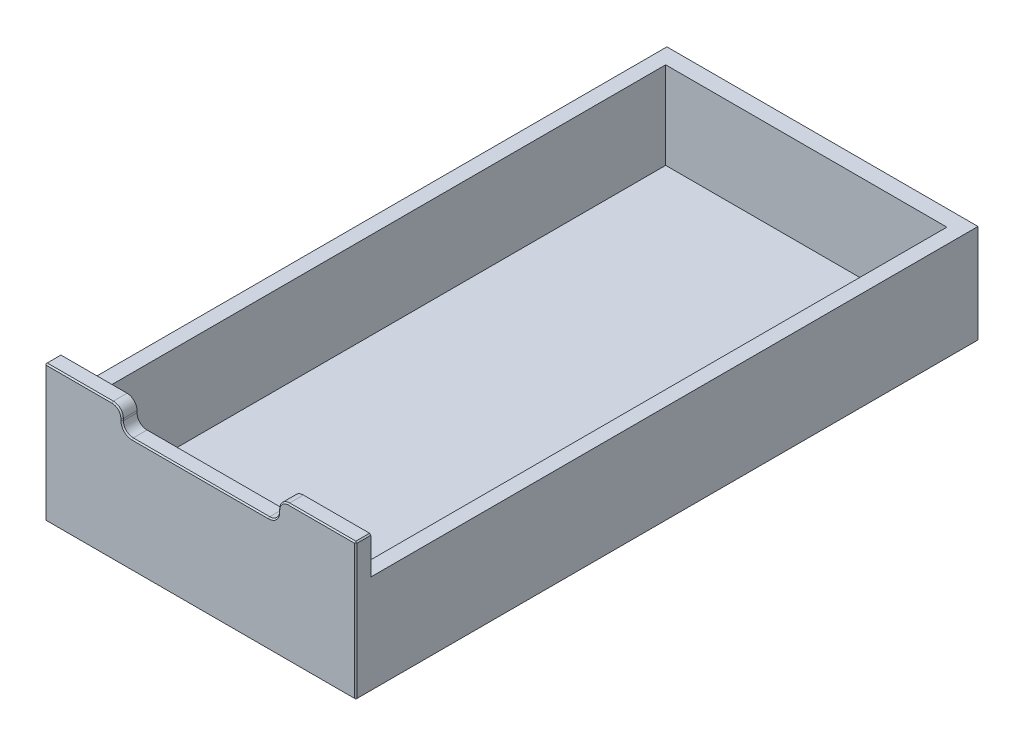
SolidWorks part; units mm, degrees
ref_plane "Front Plane" through (0, 0, 0) normal (0, 0, 1) x (1, 0, 0)
ref_plane "Top Plane" through (0, 0, 0) normal (0, 1, 0) x (1, 0, 0)
ref_plane "Right Plane" through (0, 0, 0) normal (1, 0, 0) x (0, 0, -1)
sketch "Sketch1" plane through (0, 0, 0) normal (0, 1, 0) x (1, 0, 0)
  line L1 (-125, -250) -> (125, -250)
  line L2 (-125, -250) -> (-125, 250)
  line L3 (-125, 250) -> (125, 250)
  line L4 (125, -250) -> (125, 250)
  line L5 (-125, -250) -> (125, 250) construction
  line L6 (-125, 250) -> (125, -250) construction
  point P0 (0, 0)
  dimension "D1" = 250
  dimension "D2" = 500
extrude "Boss-Extrude1" add sketch "Sketch1" along normal blind 110
sketch "Sketch2" plane through (0, 110, 0) normal (0, 1, 0) x (1, 0, 0)
  line L1 (113, -237) -> (-113, -237)
  line L2 (113, -237) -> (113, 237)
  line L3 (113, 237) -> (-113, 237)
  line L4 (-113, -237) -> (-113, 237)
  line L5 (113, -237) -> (-113, 237) construction
  line L6 (113, 237) -> (-113, -237) construction
  point P0 (0, 0)
  dimension "D1" = 226
  dimension "D2" = 474
extrude "Cut-Extrude1" cut sketch "Sketch2" against normal blind 100 contours L3 L4 L1 L2
sketch "Sketch3" plane through (0, 0, 0) normal (0, -1, 0) x (1, 0, 0)
  line L4 (125, -250) -> (125, 250)
  line L5 (125, 250) -> (-125, 250)
  line L6 (-125, 250) -> (-125, -250)
  line L7 (-125, -250) -> (125, -250)
  line L8 (125, -250) -> (125, 250)
  line L9 (125, 250) -> (-125, 250)
  line L10 (-125, 250) -> (-125, -250)
  line L11 (-125, -250) -> (125, -250)
  line L12 (113, -237) -> (113, 237)
  line L13 (-113, -237) -> (113, -237)
  line L14 (-113, 237) -> (-113, -237)
  line L15 (113, 237) -> (-113, 237)
  line L16 (113, -237) -> (113, 237)
  line L17 (-113, -237) -> (113, -237)
  line L18 (-113, 237) -> (-113, -237)
  line L19 (113, 237) -> (-113, 237)
  dimension "D1" = 0
  dimension "D2" = 0
extrude "Cut-Extrude2" cut sketch "Sketch3" against normal blind 7 contours L16 L19 L18 L17
sketch "Sketch4" plane through (125, 0, 0) normal (1, 0, 0) x (0, 0, -1)
  line L0 (-250, 110) -> (-250, 0) construction
  line L1 (293.7112, 80) -> (-238, 80)
  line L2 (293.7112, 80) -> (293.7112, 176.1049)
  line L3 (293.7112, 176.1049) -> (-238, 176.1049)
  line L4 (-238, 80) -> (-238, 176.1049)
  line L5 (-250, 0) -> (250, 0) construction
  dimension "D1" = 12
  dimension "D2" = 80
extrude "Cut-Extrude3" cut sketch "Sketch4" against normal through all
sketch "Sketch5" plane through (0, 0, 250) normal (0, 0, 1) x (1, 0, 0)
  line L1 (-62.8425, 143.5387) -> (62.8425, 143.5387)
  line L2 (-62.8425, 143.5387) -> (-62.8425, 92.4126)
  line L3 (-62.8425, 92.4126) -> (62.8425, 92.4126)
  line L4 (62.8425, 143.5387) -> (62.8425, 92.4126)
  line L5 (-62.8425, 143.5387) -> (62.8425, 92.4126) construction
  line L6 (-62.8425, 92.4126) -> (62.8425, 143.5387) construction
  point P0 (0, 117.9756)
extrude "Cut-Extrude4" cut sketch "Sketch5" against normal blind 15
fillet "Fillet1" radius 8 4 edges at (62.8425, 92.4126, 244) (62.8425, 110, 244) (-62.8425, 92.4126, 244) (-62.8425, 110, 244)
chamfer "Chamfer1" distance 1 angle 45 12 edges at (125, 55, 250) (0, 0, 250) (-125, 55, 250) (-97.9212, 110, 250) (-65.1856, 107.6569, 250) (-62.8425, 101.2063, 250) (-60.4993, 94.7557, 250) (0, 92.4126, 250) (60.4993, 94.7557, 250) (62.8425, 101.2063, 250) (65.1856, 107.6569, 250) (97.9212, 110, 250)
chamfer "Chamfer2" distance 1 angle 45 4 edges at (-125, 0, -0.5) (125, 0, -0.5) (-125, 110, 243.5) (125, 110, 243.5)
equation "\"D1@Sketch2\"=250-24"
